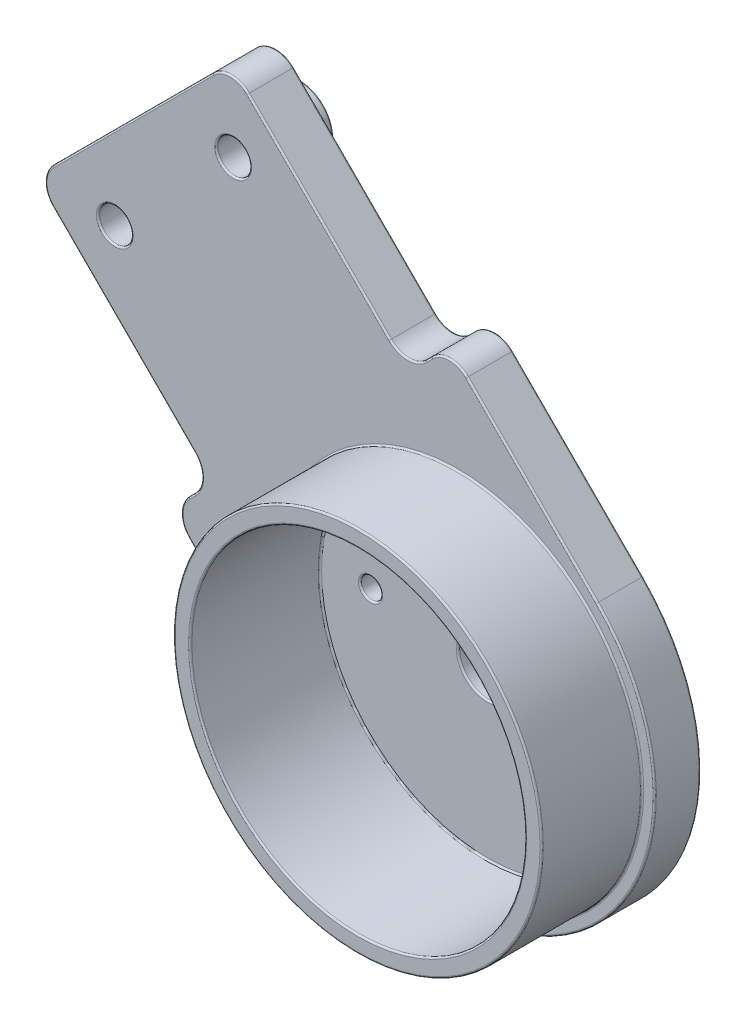
SolidWorks part; units mm, degrees
ref_plane "Front Plane" through (0, 0, 0) normal (0, 0, 1) x (1, 0, 0)
ref_plane "Top Plane" through (0, 0, 0) normal (0, 1, 0) x (1, 0, 0)
ref_plane "Right Plane" through (0, 0, 0) normal (1, 0, 0) x (0, 0, -1)
sketch "Sketch1" plane through (0, 0, 0) normal (0, 0, 1) x (1, 0, 0)
  line L0 (-100, 0) -> (100, 0) construction
  line L1 (-100, 0) -> (0, 100) construction
  line L2 (0, 100) -> (100, 0) construction
  line L3 (0, 0) -> (-50, 50) construction
  line L4 (-40, 60) -> (40, 60) construction
  line L5 (0, 100) -> (0, 60) construction
  circle A0 centre (-100, 0) radius 20
  circle A1 centre (0, 0) radius 20
  circle A2 centre (100, 0) radius 20
  dimension "D5" = 40
  dimension "D1" = 200
  dimension "D2" = 90
  dimension "D3" = 90
  dimension "D4" = 80
sketch "Sketch2" plane through (0, 0, 0) normal (0, 0, 1) x (1, 0, 0)
  line L0 (-56.5165, 43.4835) -> (-40, 60) construction
  line L1 (-100, 0) -> (0, 100) construction
  line L2 (-40, 60) -> (40, 60) construction
  line L3 (40, 60) -> (86.565, 13.435) construction
  line L4 (0, 100) -> (100, 0) construction
  line L5 (-49.4454, 36.4124) -> (-35.8579, 50)
  line L6 (-35.8579, 50) -> (35.8579, 50)
  line L7 (35.8579, 50) -> (79.4939, 6.364)
  line L8 (-63.5876, 50.5546) -> (-44.1421, 70)
  line L9 (-44.1421, 70) -> (44.1421, 70)
  line L10 (44.1421, 70) -> (93.636, 20.5061)
  line L11 (93.636, 20.5061) -> (79.4939, 6.364)
  line L12 (90.9809, 17.8509) -> (104.534, 4.6576)
  line L13 (82.1491, 9.0191) -> (95.3424, -4.534)
  line L14 (90.1005, 24.0416) -> (75.9584, 9.8995) construction
  line L15 (0, 100) -> (0, 60) construction
  line L16 (-6, 70) -> (-3.4532, 85.4203)
  line L17 (6, 70) -> (3.4532, 85.4203)
  line L18 (-63.5876, 50.5546) -> (-49.4454, 36.4124)
  circle A0 centre (100, 0) radius 10
  circle A1 centre (100, 0) radius 3.5
  arc A2 (95.3424, -4.534) -> (104.534, 4.6576) centre (100, 0) ccw
  circle A3 centre (100, 0) radius 20 construction
  circle A4 centre (79.4939, 13.435) radius 1
  circle A5 centre (100, 0) radius 6.5 construction
  circle A6 centre (86.565, 20.5061) radius 1
  circle A7 centre (0, 60) radius 1.5
  circle A8 centre (0, 84.85) radius 1.5
  arc A9 (3.4532, 85.4203) -> (-3.4532, 85.4203) centre (0, 84.85) ccw
  circle A10 centre (-50, 50) radius 1.5
  circle A11 centre (0, 84.85) radius 3.5 construction
  point P29 (106.5, 0)
  point P49 (3.5, 82)
  point P53 (0, 70)
  dimension "D4" = 20
  dimension "D5" = 7
  dimension "D9" = 2
  dimension "D12" = 3
  dimension "D17" = 3
  dimension "D3" = 27.5
  dimension "D7" = 19
  dimension "D8" = 5
  dimension "D10" = 5
  dimension "D11" = 5
  dimension "D13" = 14.85
  dimension "D15" = 6
  dimension "D16" = 6
  dimension "D1" = 10
  dimension "D2" = 10
  dimension "D6" = 3
  dimension "D14" = 2
sketch "Sketch3" plane through (0, 0, 0) normal (0, 0, 1) x (1, 0, 0)
  line L0 (-88.9571, 11.0429) -> (-50, 50)
  line L1 (-100, 0) -> (0, 100) construction
  line L2 (-50, 50) -> (-13.435, 13.435)
  line L3 (0, 0) -> (-50, 50) construction
  line L4 (-79.4939, 6.364) -> (-50, 35.8579)
  line L5 (-50, 35.8579) -> (-20.5061, 6.364)
  line L6 (-93.636, 20.5061) -> (-50, 64.1421)
  line L7 (-50, 64.1421) -> (-6.364, 20.5061)
  line L8 (-96.0281, 18.114) -> (-50, 64.1421) construction
  line L9 (-81.886, 3.9719) -> (-50, 35.8579) construction
  line L10 (-93.636, 20.5061) -> (-79.4939, 6.364)
  line L11 (-6.364, 20.5061) -> (-20.5061, 6.364)
  line L12 (-91.1612, 18.0312) -> (-104.5962, 4.5962)
  line L13 (-81.9688, 8.8388) -> (-95.4038, -4.5962)
  line L14 (-18.0312, 8.8388) -> (-4.5962, -4.5962)
  line L15 (-9.0191, 17.8509) -> (4.534, 4.6576)
  line L16 (-86.3104, 27.8317) -> (-72.1683, 13.6896) construction
  line L17 (-14.2627, 28.4049) -> (-28.4049, 14.2627) construction
  circle A0 centre (-100, 0) radius 10 construction
  circle A1 centre (-100, 0) radius 3.5
  circle A2 centre (0, 0) radius 10 construction
  circle A3 centre (0, 0) radius 3.5
  circle A4 centre (0, 0) radius 6.5
  circle A5 centre (-100, 0) radius 6.5
  circle A6 centre (0, 0) radius 20 construction
  circle A7 centre (-82.7749, 24.2962) radius 1
  circle A8 centre (-75.7038, 17.2251) radius 1
  circle A9 centre (-24.8693, 17.7983) radius 1
  circle A10 centre (-17.7983, 24.8693) radius 1
  circle A11 centre (-50, 50) radius 1.5 construction
  circle A12 centre (-50, 50) radius 1.5
  dimension "D1" = 20
  dimension "D2" = 7
  dimension "D11" = 2
  dimension "D7" = 19
  dimension "D8" = 19
  dimension "D9" = 5
  dimension "D10" = 5
  dimension "D12" = 5
  dimension "D13" = 5
  dimension "D3" = 3
  dimension "D4" = 3
  dimension "D5" = 10
  dimension "D6" = 10
sketch "Sketch4" plane through (0, 0, 0) normal (0, 0, 1) x (1, 0, 0)
  line L0 (-57.5, 93.3579) -> (57.5, 93.3579)
  line L1 (57.5, 93.3579) -> (57.5, 83.3579)
  line L2 (57.5, 83.3579) -> (44.1421, 70)
  line L3 (-44.1421, 70) -> (-57.5, 83.3579)
  line L4 (-57.5, 83.3579) -> (-57.5, 93.3579)
  line L5 (-44.1421, 70) -> (44.1421, 70) construction
  line L6 (4, 60) -> (4, 70)
  line L7 (-4, 60) -> (-4, 70)
  line L8 (-22.5, 84.85) -> (22.5, 84.85) construction
  line L9 (-22.5, 89.35) -> (22.5, 89.35)
  line L10 (-22.5, 80.35) -> (22.5, 80.35)
  line L11 (0, 100) -> (0, 60) construction
  circle A0 centre (0, 60) radius 1.5 construction
  circle A1 centre (0, 60) radius 1.5
  circle A2 centre (0, 60) radius 4
  arc A3 (-22.5, 89.35) -> (-22.5, 80.35) centre (-22.5, 84.85) ccw
  arc A4 (22.5, 80.35) -> (22.5, 89.35) centre (22.5, 84.85) ccw
  point P21 (0, 84.85)
  point P36 (0, 93.3579)
  point P39 (0, 80)
  dimension "D6" = 4.5
  dimension "D1" = 115
  dimension "D2" = 10
  dimension "D3" = 10
  dimension "D5" = 45
  dimension "D7" = 4.0079
  dimension "D4" = 2.5
sketch "Sketch5" plane through (0, 0, 0) normal (0, 0, 1) x (1, 0, 0)
  line L0 (90.9809, 17.8509) -> (104.534, 4.6576) construction
  line L1 (82.1491, 9.0191) -> (95.3424, -4.534) construction
  line L2 (-6, 70) -> (-3.4532, 85.4203) construction
  line L3 (6, 70) -> (3.4532, 85.4203) construction
  line L4 (90.9809, 17.8509) -> (104.534, 4.6576)
  line L5 (82.1491, 9.0191) -> (95.3424, -4.534)
  line L6 (-6, 70) -> (-3.4532, 85.4203)
  line L7 (6, 70) -> (3.4532, 85.4203)
  line L8 (-44.1421, 70) -> (-63.5876, 50.5546)
  line L9 (44.1421, 70) -> (-44.1421, 70)
  line L10 (93.636, 20.5061) -> (44.1421, 70)
  line L11 (79.4939, 6.364) -> (93.636, 20.5061)
  line L12 (35.8579, 50) -> (79.4939, 6.364)
  line L13 (-35.8579, 50) -> (35.8579, 50)
  line L14 (-49.4454, 36.4124) -> (-35.8579, 50)
  line L15 (-63.5876, 50.5546) -> (-49.4454, 36.4124)
  line L16 (-44.1421, 70) -> (-63.5876, 50.5546)
  line L17 (44.1421, 70) -> (6, 70)
  line L18 (93.636, 20.5061) -> (44.1421, 70)
  line L19 (79.4939, 6.364) -> (82.1491, 9.0191)
  line L20 (35.8579, 50) -> (79.4939, 6.364)
  line L21 (-35.8579, 50) -> (35.8579, 50)
  line L22 (-49.4454, 36.4124) -> (-35.8579, 50)
  line L23 (-63.5876, 50.5546) -> (-49.4454, 36.4124)
  line L24 (-6, 70) -> (-44.1421, 70)
  line L25 (90.9809, 17.8509) -> (93.636, 20.5061)
  arc A0 (95.3424, -4.534) -> (104.534, 4.6576) centre (100, 0) ccw construction
  circle A1 centre (100, 0) radius 3.5
  circle A2 centre (100, 0) radius 3.5
  circle A3 centre (100, 0) radius 10
  circle A4 centre (100, 0) radius 10
  circle A5 centre (0, 84.85) radius 1.5
  circle A6 centre (0, 84.85) radius 1.5
  circle A7 centre (0, 60) radius 1.5
  circle A8 centre (0, 60) radius 1.5
  circle A9 centre (86.565, 20.5061) radius 1
  circle A10 centre (86.565, 20.5061) radius 1
  circle A11 centre (79.4939, 13.435) radius 1
  circle A12 centre (79.4939, 13.435) radius 1
  circle A13 centre (-50, 50) radius 1.5
  circle A14 centre (-50, 50) radius 1.5
  arc A15 (3.4532, 85.4203) -> (-3.4532, 85.4203) centre (0, 84.85) ccw construction
  arc A16 (95.3424, -4.534) -> (104.534, 4.6576) centre (100, 0) ccw
  arc A17 (3.4532, 85.4203) -> (-3.4532, 85.4203) centre (0, 84.85) ccw
  dimension "D1" = 0
  dimension "D2" = 0
  dimension "D3" = 0
  dimension "D4" = 0
  dimension "D5" = 0
  dimension "D6" = 0
  dimension "D7" = 0
  dimension "D8" = 0
sketch "Sketch6" plane through (0, 0, 0) normal (0, 0, 1) x (1, 0, 0)
  line L0 (86.3882, 25.2791) -> (74.7209, 13.6118)
  line L1 (90.1005, 24.0416) -> (75.9584, 9.8995) construction
  line L2 (0, 100) -> (100, 0) construction
  line L3 (74.7209, 13.6118) -> (85.3275, 3.0052)
  line L4 (85.3275, 3.0052) -> (82.8527, 0.5303)
  line L5 (82.8527, 0.5303) -> (91.6915, -8.3085)
  line L6 (100, 0) -> (89.894, 10.106) construction
  line L7 (99.4697, 17.1473) -> (108.3085, 8.3085)
  line L8 (96.9948, 14.6725) -> (99.4697, 17.1473)
  line L9 (86.3882, 25.2791) -> (96.9948, 14.6725)
  circle A0 centre (100, 0) radius 10 construction
  circle A1 centre (100, 0) radius 10
  arc A2 (91.6915, -8.3085) -> (108.3085, 8.3085) centre (100, 0) ccw
  circle A3 centre (86.565, 20.5061) radius 1 construction
  circle A4 centre (100, 0) radius 11.75 construction
  circle A5 centre (86.565, 20.5061) radius 1
  circle A6 centre (79.4939, 13.435) radius 1 construction
  circle A7 centre (79.4939, 13.435) radius 1
  point P9 (80.5546, 19.4454)
  point P19 (111.75, 0)
  dimension "D2" = 16.5
  dimension "D3" = 15
  dimension "D4" = 12.5
  dimension "D1" = 1.75
extrude "Boss-Extrude1" add sketch "Sketch6" along normal blind 2.75
sketch "Sketch7" plane through (0, 0, 0) normal (0, 0, -1) x (-1, 0, 0)
  circle A0 centre (-100, 0) radius 10 construction
  circle A1 centre (-100, 0) radius 10
extrude "Boss-Extrude2" add sketch "Sketch7" against normal blind 1 separate body
sketch "Sketch8" plane through (0, 0, 1) normal (0, 0, 1) x (1, 0, 0)
  circle A0 centre (100, 0) radius 11
  circle A1 centre (100, 0) radius 10
  circle A2 centre (100, 0) radius 10
  dimension "D1" = 0
  dimension "D2" = 1
extrude "Boss-Extrude3" add sketch "Sketch8" along normal blind 7.75
fillet "Fillet1" radius 1.5 6 edges at (96.9948, 14.6725, 1.375) (99.4697, 17.1473, 1.375) (82.8527, 0.5303, 1.375) (85.3275, 3.0052, 1.375) (74.7209, 13.6118, 1.375) (86.3882, 25.2791, 1.375)
sketch "Sketch11" plane through (0, 0, 0) normal (0, 0, -1) x (-1, 0, 0)
  circle A0 centre (-86.565, 20.5061) radius 1 construction
  circle A1 centre (-79.4939, 13.435) radius 1 construction
  circle A2 centre (-86.565, 20.5061) radius 1
  circle A3 centre (-79.4939, 13.435) radius 1
  circle A4 centre (-86.565, 20.5061) radius 2
  circle A5 centre (-79.4939, 13.435) radius 2
  dimension "D1" = 1
extrude "Boss-Extrude4" add sketch "Sketch11" along normal blind 1.25
sketch "Sketch12" plane through (0, 0, 0) normal (0, 0, -1) x (-1, 0, 0)
  circle A0 centre (-100, 0) radius 1.75
  dimension "D1" = 3.5
extrude "Cut-Extrude1" cut sketch "Sketch12" against normal up to surface (1 mm away) up to face at (90, 0, 1)
sketch "Sketch13" plane through (0, 0, 0) normal (0, 0, -1) x (-1, 0, 0)
  circle A0 centre (-100, 0) radius 1.75 construction
  circle A1 centre (-100, 0) radius 1.75
  circle A2 centre (-100, 0) radius 3.45
  dimension "D1" = 6.9
extrude "Boss-Extrude5" add sketch "Sketch13" along normal blind 4.25
sketch "Sketch14" plane through (0, 0, 0) normal (0, 0, -1) x (-1, 0, 0)
  line L0 (-100, 0) -> (-93.0204, 0.5334) construction
  circle A0 centre (-93.0204, 0.5334) radius 0.625
  circle A1 centre (-103.0279, -6.3113) radius 0.625
  circle A2 centre (-103.9518, 5.7779) radius 0.625
  point P11 (-100, 0)
  dimension "D1" = 1.25
  dimension "D2" = 7
  dimension "D3" = 3
extrude "Cut-Extrude2" cut sketch "Sketch14" against normal up to surface (1 mm away) up to face at (98.25, 0, 1)
fillet "Fillet2" radius 0.1 50 edges at (103.3268, 5.7779, 1) (103.3268, 5.7779, 0) (102.4029, -6.3113, 1) (102.4029, -6.3113, 0) (92.3954, 0.5334, 0) (92.3954, 0.5334, 1) (98.25, 0, -4.25) (96.55, 0, -4.25) (98.25, 0, 1) (77.4939, 13.435, -1.25) (78.4939, 13.435, -1.25) (85.565, 20.5061, -1.25) (84.565, 20.5061, -1.25) (90, 0, 1) (110, 0, 8.75) (111, 0, 8.75) (111, 0, 2.75) (80.4939, 13.435, 2.75) (87.565, 20.5061, 2.75) (80.5546, 19.4454, 0) (80.0242, 8.3085, 0) (84.0901, 1.7678, 0) (87.8024, -4.4194, 0) (108.3085, -8.3085, 0) (104.4194, 12.1976, 0) (98.2322, 15.9099, 0) (91.6915, 19.9758, 2.75) (80.5546, 19.4454, 2.75) (80.0242, 8.3085, 2.75) (84.0901, 1.7678, 2.75) (87.8024, -4.4194, 2.75) (108.3085, -8.3085, 2.75) (104.4194, 12.1976, 2.75) (98.2322, 15.9099, 2.75) (86.3882, 24.6577, 0) (75.3423, 13.6118, 0) (83.474, 0.5303, 0) (99.4697, 16.526, 0) (86.3882, 24.6577, 2.75) (75.3423, 13.6118, 2.75) (83.474, 0.5303, 2.75) (99.4697, 16.526, 2.75) (96.9948, 15.2938, 0) (96.9948, 15.2938, 2.75) (84.7062, 3.0052, 0) (84.7062, 3.0052, 2.75) (88.565, 20.5061, 0) (81.4939, 13.435, 0) (103.45, 0, 0) (91.6915, 19.9758, 0)
